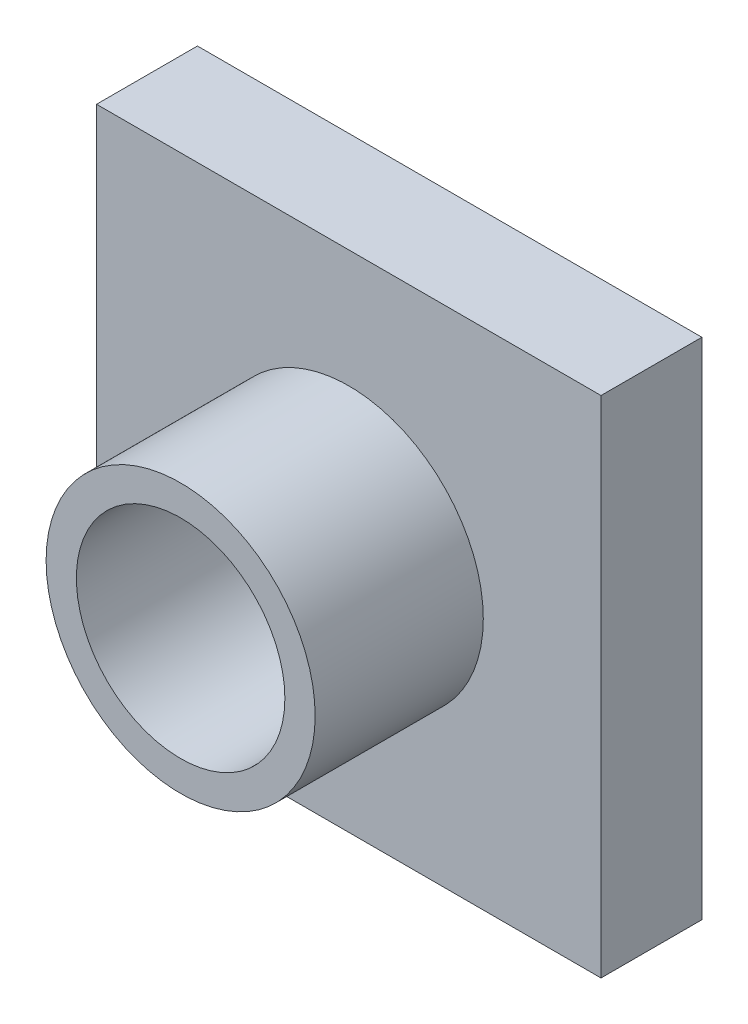
SolidWorks part; units mm, degrees
ref_plane "Front Plane" through (0, 0, 0) normal (0, 0, 1) x (1, 0, 0)
ref_plane "Top Plane" through (0, 0, 0) normal (0, 1, 0) x (1, 0, 0)
ref_plane "Right Plane" through (0, 0, 0) normal (1, 0, 0) x (0, 0, -1)
sketch "Sketch3" plane through (0, 0, 0) normal (0, 0, 1) x (1, 0, 0)
  line L1 (-7.5, -7.5) -> (7.5, -7.5)
  line L2 (-7.5, -7.5) -> (-7.5, 7.5)
  line L3 (-7.5, 7.5) -> (7.5, 7.5)
  line L4 (7.5, -7.5) -> (7.5, 7.5)
  line L5 (-7.5, -7.5) -> (7.5, 7.5) construction
  line L6 (-7.5, 7.5) -> (7.5, -7.5) construction
  point P0 (0, 0)
  dimension "D1" = 15
  dimension "D2" = 15
extrude "Boss-Extrude1" add sketch "Sketch3" along normal blind 3 contours L3 L4 L1 L2
sketch "Sketch4" plane through (0, 0, 3) normal (0, 0, 1) x (1, 0, 0)
  circle A0 centre (0, 0) radius 4
extrude "Boss-Extrude2" add sketch "Sketch4" along normal blind 5
sketch "Sketch5" plane through (0, 0, 8) normal (0, 0, 1) x (1, 0, 0)
  circle A0 centre (0, 0) radius 3.1
extrude "Cut-Extrude1" cut sketch "Sketch5" against normal blind 4.5
